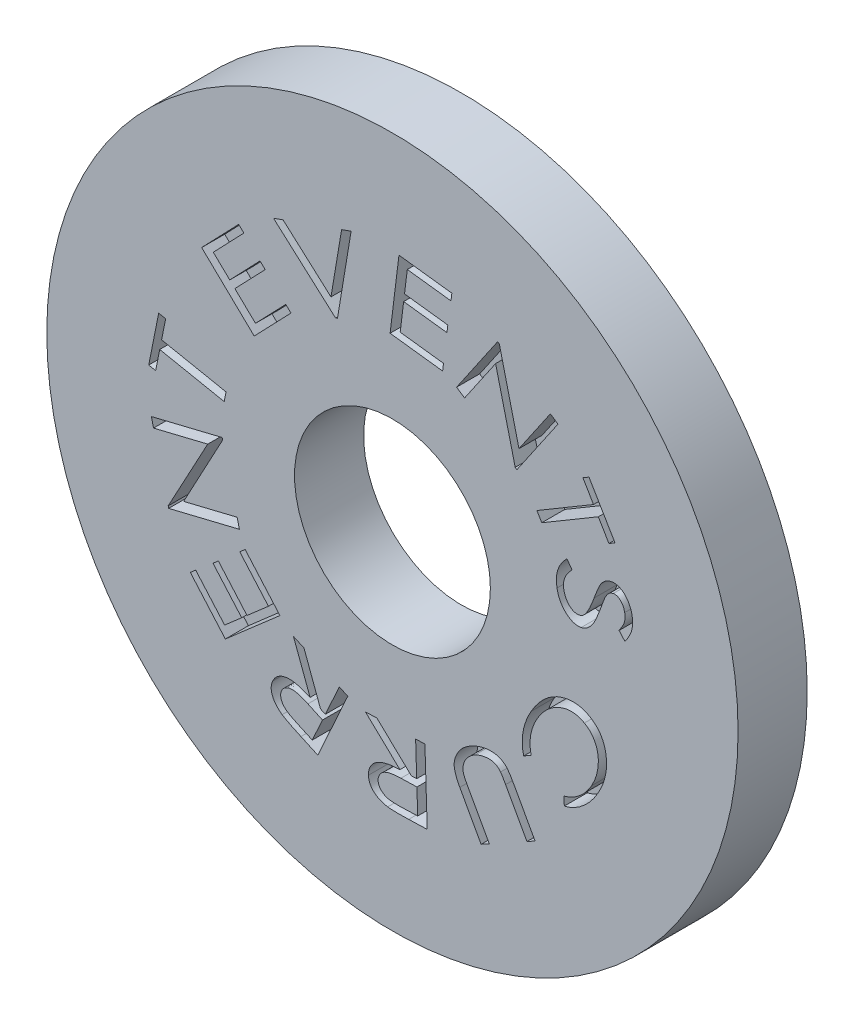
SolidWorks part; units mm, degrees
material "ABS PC"
ref_plane "Front Plane" through (0, 0, 0) normal (0, 0, 1) x (1, 0, 0)
ref_plane "Top Plane" through (0, 0, 0) normal (0, 1, 0) x (1, 0, 0)
ref_plane "Right Plane" through (0, 0, 0) normal (1, 0, 0) x (0, 0, -1)
sketch "Sketch1" plane through (0, 0, 0) normal (0, 0, 1) x (1, 0, 0)
  circle A1 centre (0, 0) radius 15
  dimension "D1" = 30
extrude "Boss-Extrude1" add sketch "Sketch1" along normal blind 3
sketch "Sketch3" plane through (0, 0, 3) normal (0, 0, 1) x (1, 0, 0)
  circle A0 centre (0, 0) radius 4.25
  dimension "D1" = 8.5
extrude "Cut-Extrude1" cut sketch "Sketch3" against normal through all
sketch "Sketch6" plane through (0, 0, 3) normal (0, 0, 1) x (1, 0, 0)
  circle A0 centre (0, 0) radius 7.5
  dimension "D1" = 15
sketch "Sketch7" plane through (0, 0, 3) normal (0, 0, 1) x (1, 0, 0)
  text T0 "CURRENT EVENTS" font "Century Gothic" height 3.175
extrude "Cut-Extrude3" cut sketch "Sketch7" against normal blind 1
